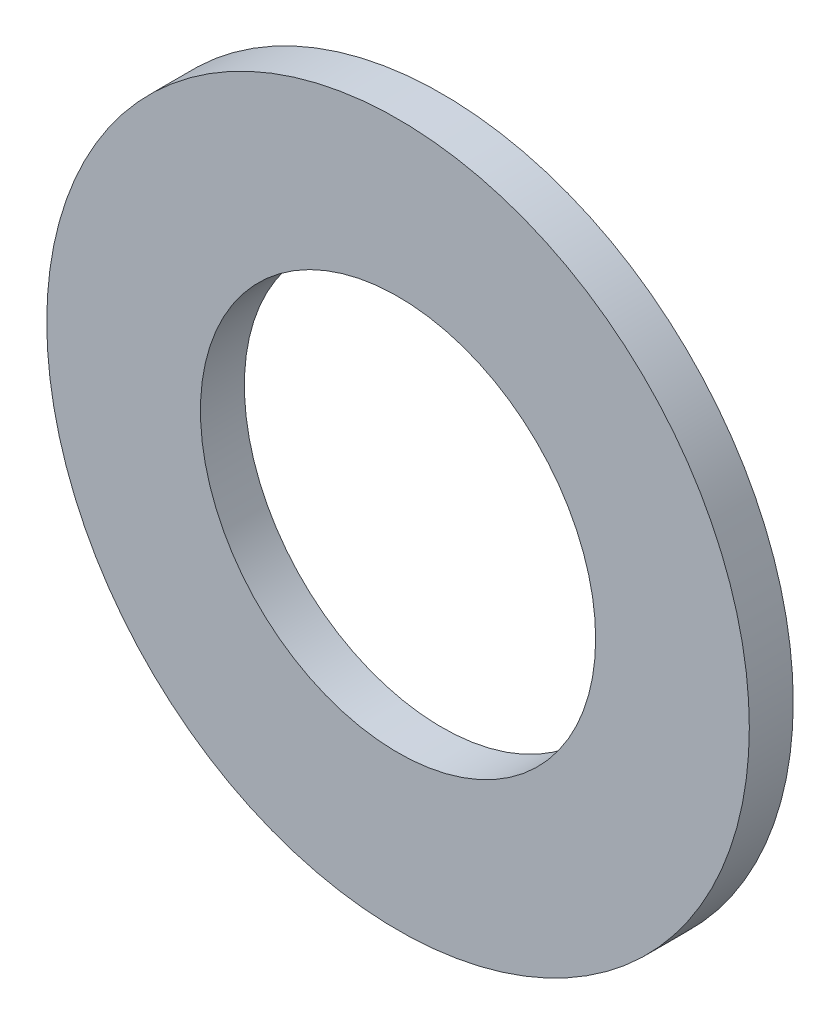
SolidWorks part; units mm, degrees
ref_plane "Front Plane" through (0, 0, 0) normal (0, 0, 1) x (1, 0, 0)
ref_plane "Top Plane" through (0, 0, 0) normal (0, 1, 0) x (1, 0, 0)
ref_plane "Right Plane" through (0, 0, 0) normal (1, 0, 0) x (0, 0, -1)
sketch "Sketch1" plane through (0, 0, 0) normal (0, 0, 1) x (1, 0, 0)
  circle A0 centre (-31.1719, 18.6721) radius 8
extrude "Boss-Extrude1" add sketch "Sketch1" along normal blind 1
sketch "Sketch2" plane through (0, 0, 1) normal (0, 0, 1) x (1, 0, 0)
  circle A0 centre (-31.1719, 18.6721) radius 4.5
  circle A1 centre (-31.1719, 18.6721) radius 8 construction
  dimension "D1" = 0
  dimension "D2" = 9
extrude "Cut-Extrude1" cut sketch "Sketch2" against normal blind 1
